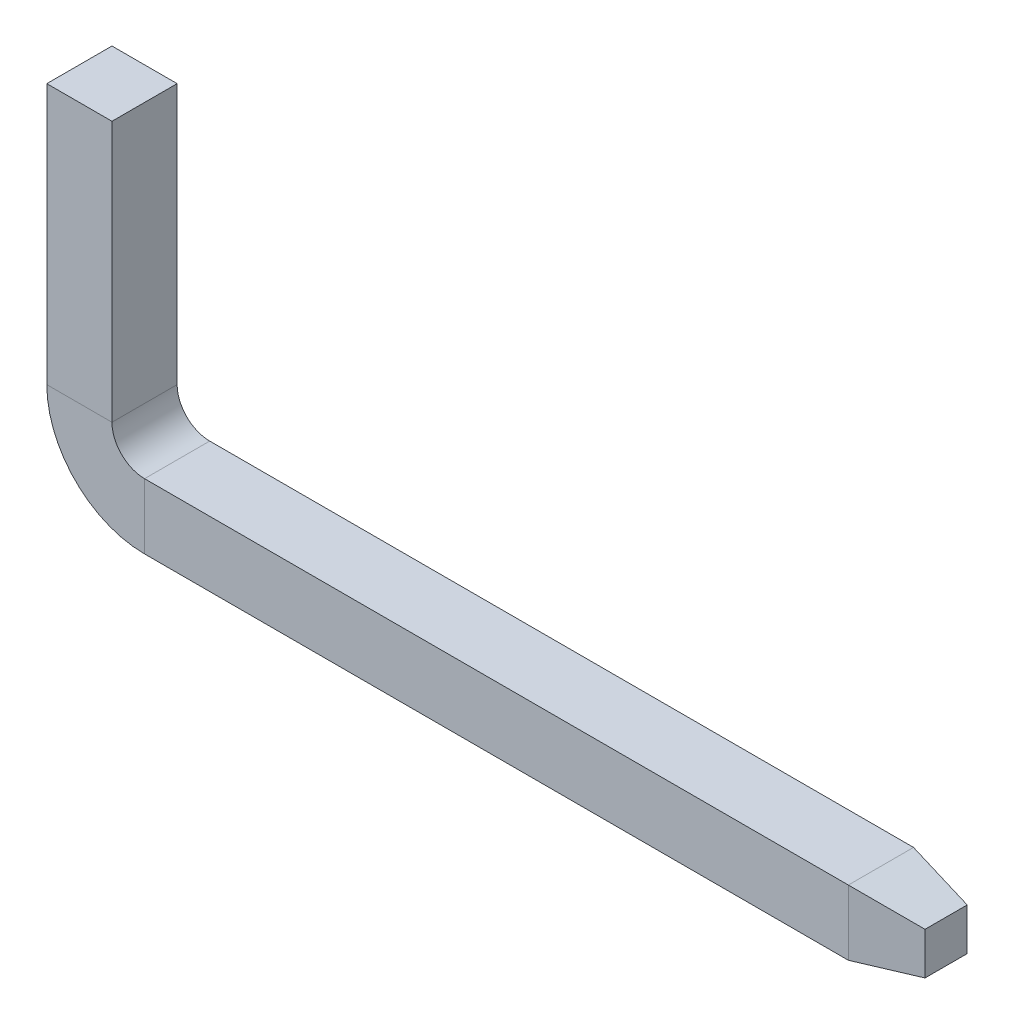
SolidWorks part; units mm, degrees
ref_plane "Front Plane" through (0, 0, 0) normal (0, 0, 1) x (1, 0, 0)
ref_plane "Top Plane" through (0, 0, 0) normal (0, 1, 0) x (1, 0, 0)
ref_plane "Right Plane" through (0, 0, 0) normal (1, 0, 0) x (0, 0, -1)
sketch "Sketch1" plane through (0, 0, 0) normal (0, 1, 0) x (1, 0, 0)
  line L1 (-0.25, -0.25) -> (0.25, -0.25)
  line L2 (-0.25, -0.25) -> (-0.25, 0.25)
  line L3 (-0.25, 0.25) -> (0.25, 0.25)
  line L4 (0.25, -0.25) -> (0.25, 0.25)
  line L5 (-0.25, -0.25) -> (0.25, 0.25) construction
  line L6 (-0.25, 0.25) -> (0.25, -0.25) construction
  point P0 (0, 0)
  dimension "D1" = 0.5
sketch "Sketch2" plane through (0, 0, 0) normal (0, 0, 1) x (1, 0, 0)
  line L0 (0, 0) -> (0, -2)
  line L1 (0.5, -2.5) -> (5.9, -2.5)
  arc A0 (0, -2) -> (0.5, -2.5) centre (0.5, -2) ccw
  point P6 (0, -2.5)
  dimension "D3" = 0.5
  dimension "D1" = 2.5
  dimension "D2" = 5.9
ref_plane "Plane1" through (5.9, 0, 0) normal (1, 0, 0) x (0, 0, -1)
sweep "Sweep1" add profiles "Sketch1" path "Sketch2"
sketch "Sketch4" plane through (5.9, 0, 0) normal (1, 0, 0) x (0, 0, -1)
  line L4 (0.25, -2.25) -> (-0.25, -2.25)
  line L5 (-0.25, -2.25) -> (-0.25, -2.75)
  line L6 (-0.25, -2.75) -> (0.25, -2.75)
  line L7 (0.25, -2.75) -> (0.25, -2.25)
  line L8 (0.25, -2.25) -> (-0.25, -2.25)
  line L9 (-0.25, -2.25) -> (-0.25, -2.75)
  line L10 (-0.25, -2.75) -> (0.25, -2.75)
  line L11 (0.25, -2.75) -> (0.25, -2.25)
  dimension "D1" = 0
extrude "Boss-Extrude1" add sketch "Sketch4" along normal blind 0.5 draft 10
